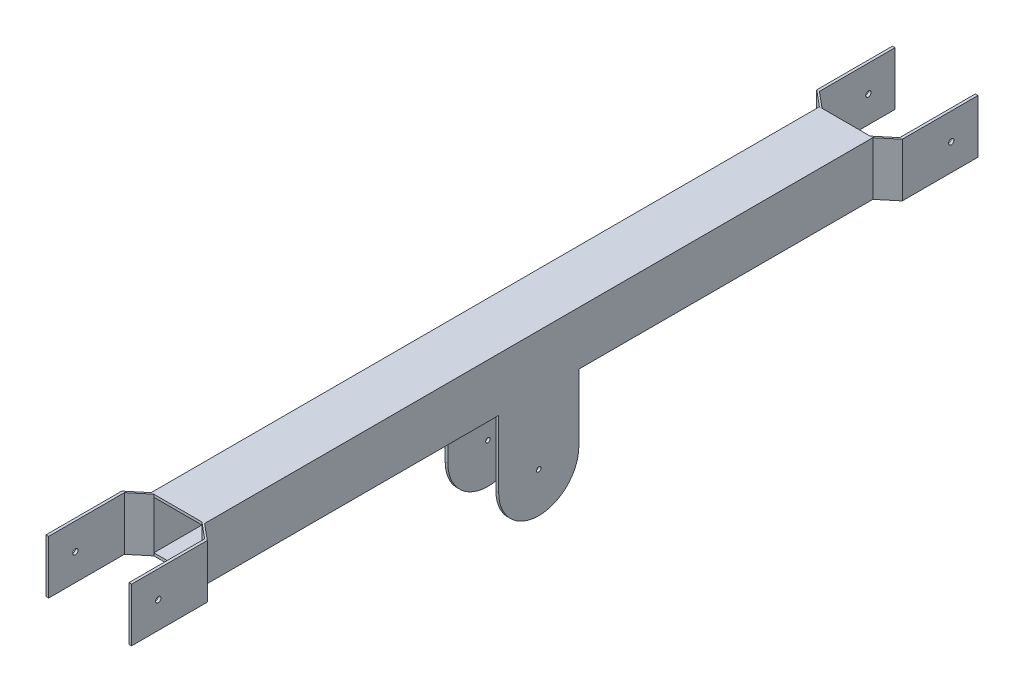
SolidWorks part; units mm, degrees
material "1.0036 (S235JRG1)"
ref_plane "Ön Düzlem" through (0, 0, 0) normal (0, 0, 1) x (1, 0, 0)
ref_plane "Üst Düzlem" through (0, 0, 0) normal (0, 1, 0) x (1, 0, 0)
ref_plane "Sağ Düzlem" through (0, 0, 0) normal (1, 0, 0) x (0, 0, -1)
sketch "Çizim1" plane through (0, 0, 0) normal (0, 0, 1) x (1, 0, 0)
  line L1 (0, 0) -> (120, 0)
  line L2 (0, 0) -> (0, 120)
  line L3 (0, 120) -> (120, 120)
  line L4 (120, 0) -> (120, 120)
  line L5 (114, 114) -> (6, 114)
  line L6 (114, 114) -> (114, 6)
  line L7 (114, 6) -> (6, 6)
  line L8 (6, 114) -> (6, 6)
  dimension "D1" = 120
  dimension "D2" = 120
  dimension "D3" = 6
  dimension "D4" = 6
  dimension "D5" = 6
  dimension "D6" = 6
extrude "Yükseklik-Ekstrüzyon1" add sketch "Çizim1" against normal blind 1700
sketch "Çizim2" plane through (0, 120, 0) normal (0, 1, 0) x (1, 0, 0)
  line L0 (60, 1700) -> (60, 1801.2229) construction
  line L1 (120, 1700) -> (0, 1700) construction
  line L2 (0, 1700) -> (-36, 1730)
  line L3 (-36, 1730) -> (-36, 1900)
  line L4 (6, 1700) -> (-30, 1730)
  line L5 (-30, 1730) -> (-30, 1900)
  line L6 (-30, 1900) -> (-36, 1900)
  line L7 (0, 1700) -> (6, 1700)
  line L8 (150, 1900) -> (156, 1900)
  line L9 (150, 1730) -> (150, 1900)
  line L10 (156, 1730) -> (156, 1900)
  line L11 (120, 1700) -> (156, 1730)
  line L12 (114, 1700) -> (120, 1700)
  line L13 (114, 1700) -> (150, 1730)
  dimension "D1" = 30
  dimension "D2" = 30
  dimension "D3" = 6
  dimension "D4" = 6
  dimension "D5" = 170
  dimension "D6" = 170
extrude "Yükseklik-Ekstrüzyon2" add sketch "Çizim2" against normal blind 120 separate body
sketch "Çizim3" plane through (156, 0, 0) normal (1, 0, 0) x (0, 0, -1)
  line L0 (1730, 120) -> (1900, 120) construction
  line L1 (1900, 0) -> (1900, 120) construction
  line L2 (1840, 120) -> (1900, 120)
  line L3 (1900, 120) -> (1900, 0)
  line L4 (1900, 0) -> (1840, 0)
  circle A0 centre (1840, 60) radius 6
  circle A1 centre (1840, 60) radius 60
  dimension "D1" = 12
  dimension "D3" = 60
  dimension "D2" = 60
extrude "Kes-Ekstrüzyon3" cut sketch "Çizim3" against normal blind 264 contours A0
sketch "Çizim4" plane through (0, 120, 0) normal (0, 1, 0) x (1, 0, 0)
  line L0 (120, 1700) -> (120, 0) construction
  line L1 (0, 0) -> (120, 0)
  line L2 (0, 0) -> (0, 200)
  line L3 (0, 200) -> (120, 200)
  line L4 (120, 0) -> (120, 200)
  dimension "D1" = 200
extrude "Kes-Ekstrüzyon4" cut sketch "Çizim4" against normal blind 184
sketch "Çizim5" plane through (0, 120, 0) normal (0, 1, 0) x (1, 0, 0)
  line L0 (0, 950) -> (120, 950) construction
  line L1 (0, 1700) -> (0, 200) construction
  line L2 (120, 1700) -> (120, 200) construction
ref_plane "Düzlem1" through (0, 0, -950) normal (0, 0, 1) x (1, 0, 0)
mirror "Aynalama1" about plane through (0, 0, -950) normal (0, 0, 1) of "Yükseklik-Ekstrüzyon2"
mirror "Aynalama2" about plane through (0, 0, -950) normal (0, 0, 1) of "Kes-Ekstrüzyon3"
sketch "Çizim6" plane through (120, 0, 0) normal (1, 0, 0) x (0, 0, -1)
  line L0 (860, 0) -> (860, -150)
  line L1 (1700, 0) -> (200, 0) construction
  line L2 (1040, -150) -> (1040, 0)
  line L3 (1040, 0) -> (860, 0)
  arc A0 (860, -150) -> (1040, -150) centre (950, -150) ccw
  dimension "D1" = 90
  dimension "D2" = 150
  dimension "D3" = 950
extrude "Yükseklik-Ekstrüzyon3" add sketch "Çizim6" against normal blind 6
sketch "Çizim7" plane through (0, 0, 0) normal (-1, 0, 0) x (0, 0, 1)
  line L0 (-1040, 0) -> (-860, 0)
  line L1 (-860, 0) -> (-860, -150)
  line L2 (-1040, -150) -> (-1040, 0)
  arc A0 (-860, -150) -> (-1040, -150) centre (-950, -150) cw
extrude "Yükseklik-Ekstrüzyon4" add sketch "Çizim7" against normal blind 6
sketch "Çizim8" plane through (120, 0, 0) normal (1, 0, 0) x (0, 0, -1)
  circle A0 centre (950, -150) radius 5
  dimension "D1" = 10
extrude "Kes-Ekstrüzyon5" cut sketch "Çizim8" against normal blind 181
